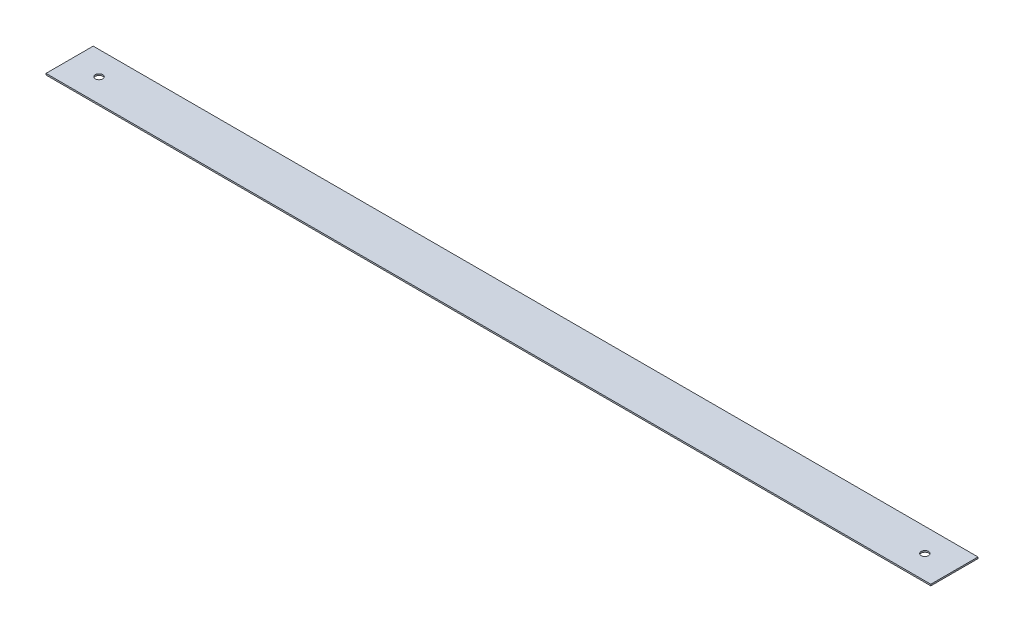
SolidWorks part; units mm, degrees
ref_plane "Front Plane" through (0, 0, 0) normal (0, 0, 1) x (1, 0, 0)
ref_plane "Top Plane" through (0, 0, 0) normal (0, 1, 0) x (1, 0, 0)
ref_plane "Right Plane" through (0, 0, 0) normal (1, 0, 0) x (0, 0, -1)
sketch "Sketch1" plane through (0, 0, 0) normal (0, 1, 0) x (1, 0, 0)
  line L1 (0, 0) -> (7620, 0)
  line L2 (0, 0) -> (0, -406.4)
  line L3 (0, -406.4) -> (7620, -406.4)
  line L4 (7620, 0) -> (7620, -406.4)
  circle A0 centre (254, -203.2) radius 31.75
  circle A1 centre (7366, -203.2) radius 31.75
  point P5 (0, -203.2)
  point P6 (254, -203.2)
  point P9 (7620, -203.2)
  point P10 (7366, -203.2)
  dimension "D4" = 63.5
  dimension "D5" = 63.5
  dimension "D1" = 406.4
  dimension "D2" = 7620
  dimension "D3" = 254
  dimension "D6" = 254
extrude "Boss-Extrude1" add sketch "Sketch1" along normal blind 12.7
